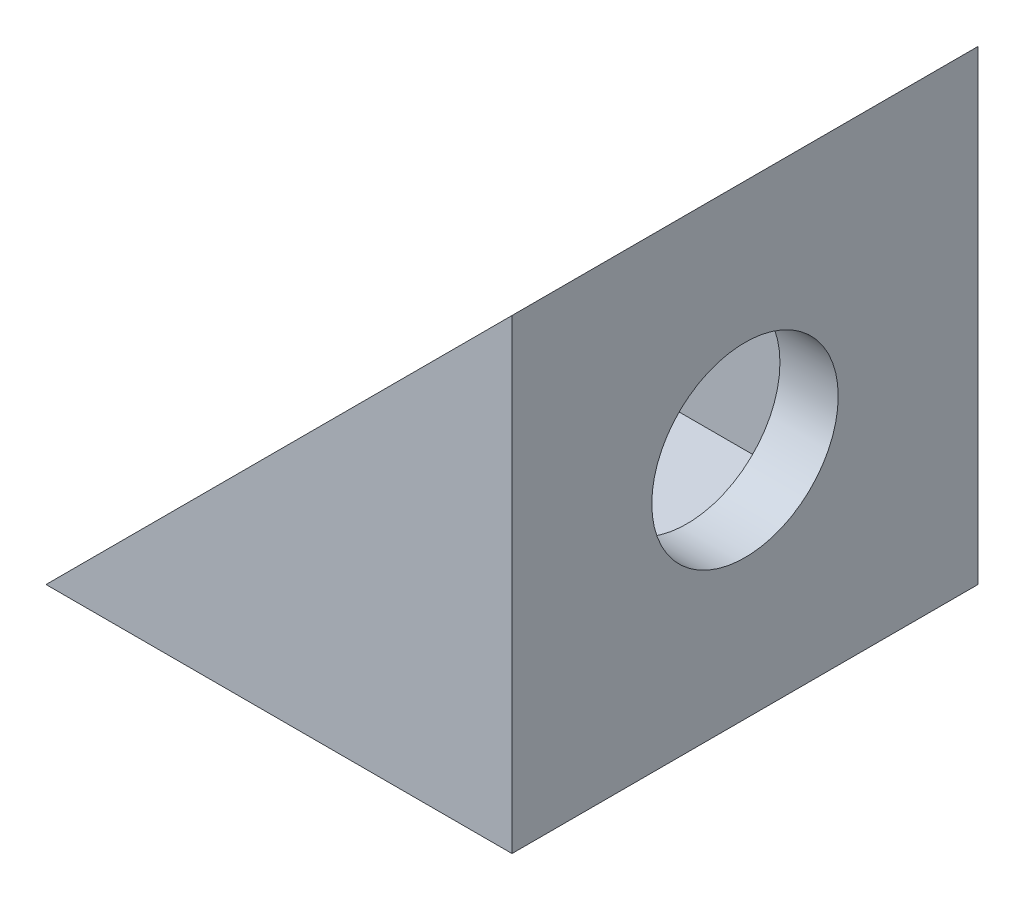
SolidWorks part; units mm, degrees
ref_plane "Front Plane" through (0, 0, 0) normal (0, 0, 1) x (1, 0, 0)
ref_plane "Top Plane" through (0, 0, 0) normal (0, 1, 0) x (1, 0, 0)
ref_plane "Right Plane" through (0, 0, 0) normal (1, 0, 0) x (0, 0, -1)
sketch "Sketch1" plane through (0, 0, 0) normal (0, 1, 0) x (1, 0, 0)
  line L1 (-10, 10) -> (10, 10)
  line L2 (-10, 10) -> (-10, -10)
  line L3 (-10, -10) -> (10, -10)
  line L4 (10, 10) -> (10, -10)
  line L5 (-10, 10) -> (10, -10) construction
  line L6 (-10, -10) -> (10, 10) construction
  point P0 (0, 0)
  dimension "D1" = 20
  dimension "D2" = 20
extrude "Boss-Extrude1" add sketch "Sketch1" along normal blind 20
sketch "Sketch2" plane through (0, 0, 10) normal (0, 0, 1) x (1, 0, 0)
  line L0 (-10, 0) -> (10, 20)
  line L1 (10, 20) -> (-10, 20)
  line L2 (-10, 20) -> (-10, 0)
extrude "Cut-Extrude1" cut sketch "Sketch2" against normal through all both and the other way through all
sketch "Sketch3" plane through (10, 0, 0) normal (1, 0, 0) x (0, 0, -1)
  line L0 (-10, 10) -> (10, 10) construction
  line L1 (-10, 20) -> (-10, 0) construction
  line L2 (10, 20) -> (10, 0) construction
  circle A0 centre (0, 10) radius 4
  point P8 (0, 10)
  dimension "D1" = 8
extrude "Cut-Extrude2" cut sketch "Sketch3" against normal through all contours A0
sketch "Sketch4" plane through (0, 0, 0) normal (0, -1, 0) x (1, 0, 0)
  circle A0 centre (0, 0) radius 4
  dimension "D1" = 8
extrude "Cut-Extrude3" cut sketch "Sketch4" against normal through all
ref_plane "Plane1" through (0, 20, 0) normal (0, 1, 0) x (1, 0, 0)
sketch "Sketch5" plane through (0, 20, 0) normal (0, 1, 0) x (1, 0, 0)
  line L1 (-7.5, -7.5) -> (7.5, -7.5)
  line L2 (-7.5, -7.5) -> (-7.5, 7.5)
  line L3 (-7.5, 7.5) -> (7.5, 7.5)
  line L4 (7.5, -7.5) -> (7.5, 7.5)
  line L5 (-7.5, -7.5) -> (7.5, 7.5) construction
  line L6 (-7.5, 7.5) -> (7.5, -7.5) construction
  point P0 (0, 0)
  dimension "D1" = 15
extrude "Cut-Extrude5" cut sketch "Sketch5" against normal offset from surface (17.5 mm away) 2.5 up to face at (0, 0, -4)
